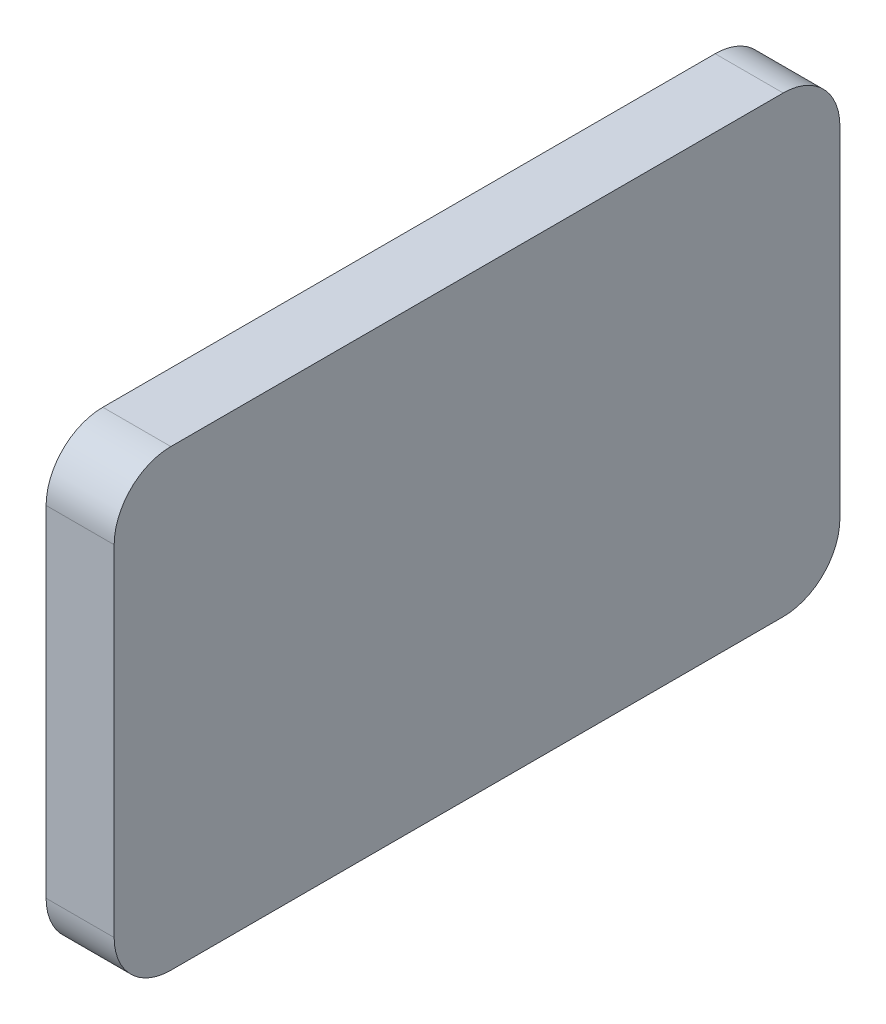
SolidWorks part; units mm, degrees
material "BUTYL"
ref_plane "前视基准面" through (0, 0, 0) normal (0, 0, 1) x (1, 0, 0)
ref_plane "上视基准面" through (0, 0, 0) normal (0, 1, 0) x (1, 0, 0)
ref_plane "右视基准面" through (0, 0, 0) normal (1, 0, 0) x (0, 0, -1)
sketch "草图1" plane through (0, 0, 0) normal (1, 0, 0) x (0, 0, -1)
  line L1 (-27, 20) -> (27, 20)
  line L2 (-32, 15) -> (-32, -15)
  line L3 (-27, -20) -> (27, -20)
  line L4 (32, 15) -> (32, -15)
  line L5 (-32, 20) -> (32, -20) construction
  line L6 (-32, -20) -> (32, 20) construction
  arc A0 (27, 20) -> (32, 15) centre (27, 15) cw
  arc A1 (27, -20) -> (32, -15) centre (27, -15) ccw
  arc A2 (-27, -20) -> (-32, -15) centre (-27, -15) cw
  arc A3 (-32, 15) -> (-27, 20) centre (-27, 15) cw
  point P0 (0, 0)
  dimension "D3" = 5
  dimension "D1" = 64
  dimension "D2" = 40
extrude "凸台-拉伸1" add sketch "草图1" along normal blind 6
